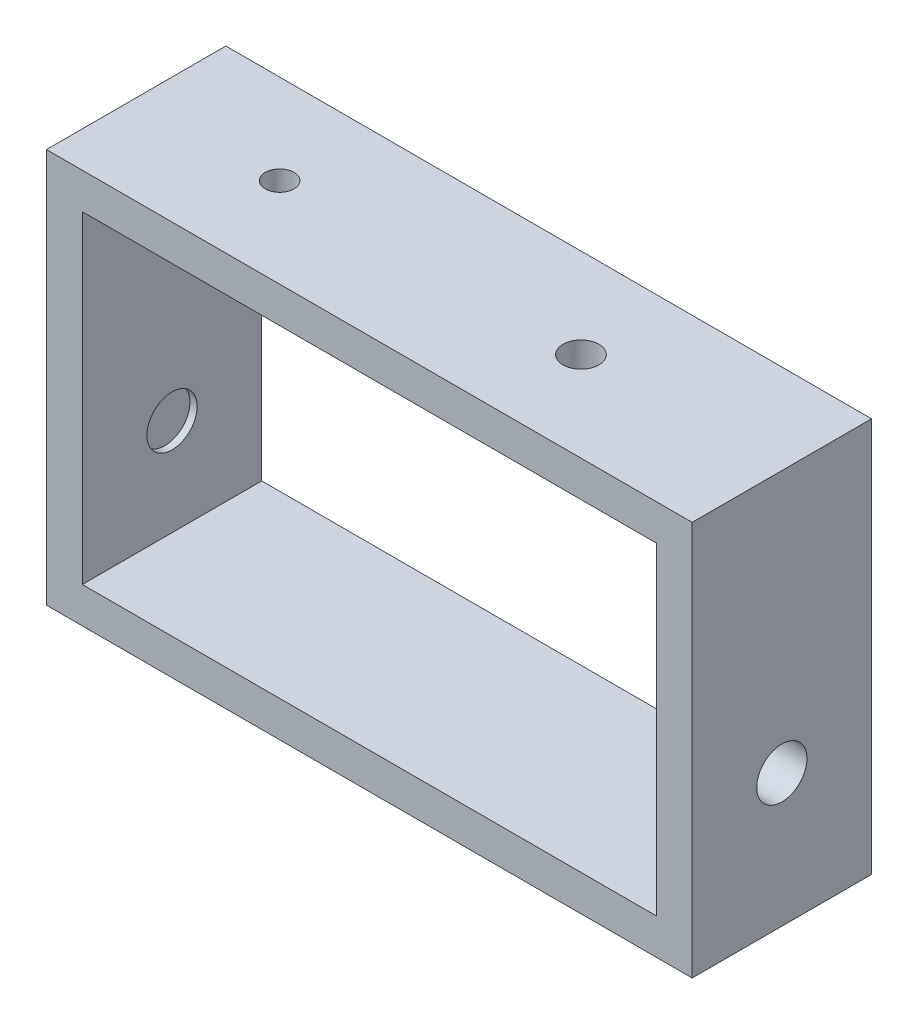
SolidWorks part; units mm, degrees
ref_plane "Alzado" through (0, 0, 0) normal (0, 0, 1) x (1, 0, 0)
ref_plane "Planta" through (0, 0, 0) normal (0, 1, 0) x (1, 0, 0)
ref_plane "Vista lateral" through (0, 0, 0) normal (1, 0, 0) x (0, 0, -1)
sketch "Croquis2" plane through (0, 0, 0) normal (0, 0, 1) x (1, 0, 0)
  line L0 (5, 50) -> (85, 50)
  line L1 (0, 0) -> (90, 0)
  line L2 (0, 0) -> (0, 55)
  line L3 (0, 55) -> (90, 55)
  line L4 (90, 0) -> (90, 55)
  line L5 (85, 5) -> (85, 50)
  line L6 (5, 5) -> (85, 5)
  line L7 (5, 5) -> (5, 50)
  dimension "D1" = 55
  dimension "D2" = 90
  dimension "D3" = 5
extrude "Saliente-Extruir2" add sketch "Croquis2" along normal mid plane 25
sketch "Croquis4" plane through (90, 0, 0) normal (1, 0, 0) x (0, 0, -1)
  line L0 (-12.5, 0) -> (12.5, 0) construction
  circle A0 centre (0, 18.5) radius 3.5
  point P2 (0, 0)
  dimension "D2" = 7
  dimension "D1" = 18.5
extrude "Cortar-Extruir2" cut sketch "Croquis4" against normal blind 86 contours A0
sketch "Croquis5" plane through (0, 55, 0) normal (0, 1, 0) x (1, 0, 0)
  line L0 (0, -12.5) -> (0, 12.5) construction
  circle A0 centre (20, 0) radius 2
  circle A1 centre (62, 0) radius 2.5
  point P4 (0, 0)
  point P7 (0, 0)
  point P9 (46.6178, -9.0402)
  dimension "D3" = 4
  dimension "D4" = 5
  dimension "D1" = 20
  dimension "D2" = 62
extrude "Cortar-Extruir4" cut sketch "Croquis5" against normal blind 10
